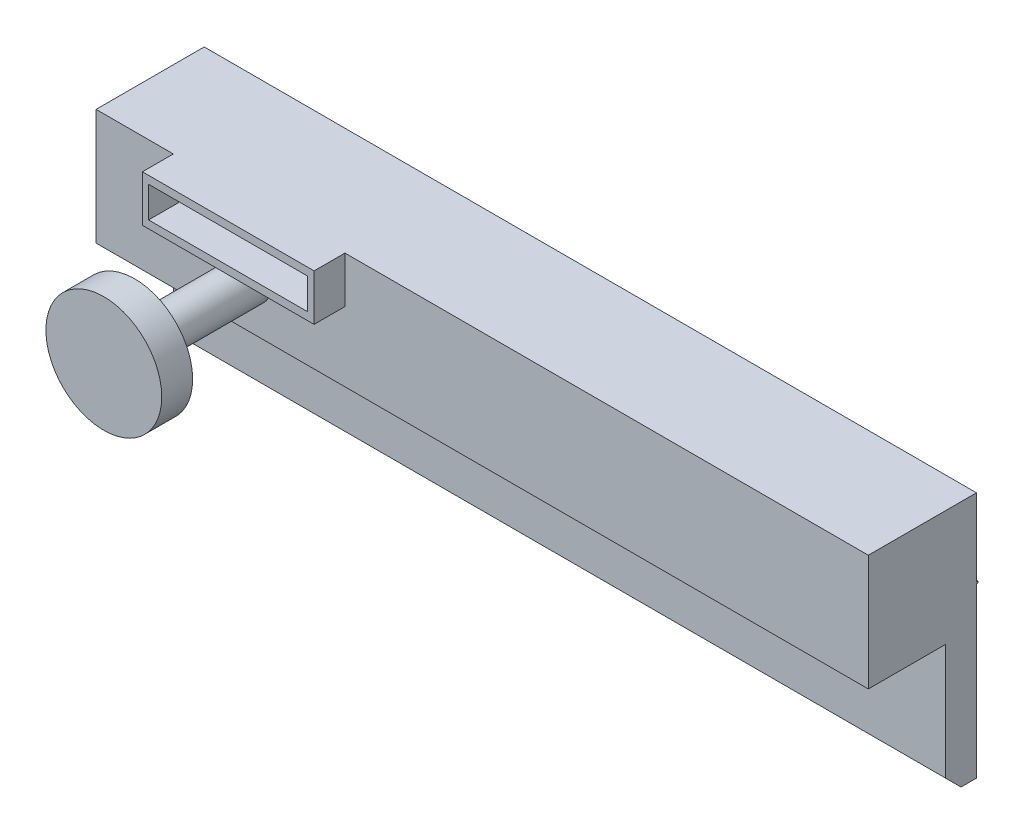
SolidWorks part; units mm, degrees
ref_plane "Front Plane" through (0, 0, 0) normal (0, 0, 1) x (1, 0, 0)
ref_plane "Top Plane" through (0, 0, 0) normal (0, 1, 0) x (1, 0, 0)
ref_plane "Right Plane" through (0, 0, 0) normal (1, 0, 0) x (0, 0, -1)
sketch "Sketch1" plane through (0, 0, 0) normal (0, 0, 1) x (1, 0, 0)
  line L1 (0, 0) -> (127, 0)
  line L2 (0, 0) -> (0, 40.64)
  line L3 (0, 40.64) -> (127, 40.64)
  line L4 (127, 0) -> (127, 40.64)
  dimension "D1" = 40.64
  dimension "D2" = 127
extrude "Boss-Extrude1" add sketch "Sketch1" along normal blind 5.08
chamfer "Chamfer3" distance 2.54 angle 45 1 edges at (63.5, 0, 5.08)
sketch "Sketch6" plane through (0, 0, 5.08) normal (0, 0, 1) x (1, 0, 0)
  line L0 (127, 2.54) -> (127, 40.64) construction
  line L1 (0, 40.64) -> (127, 40.64)
  line L2 (0, 40.64) -> (0, 21.59)
  line L3 (0, 21.59) -> (127, 21.59)
  line L4 (127, 40.64) -> (127, 21.59)
  dimension "D1" = 19.05
extrude "Boss-Extrude4" add sketch "Sketch6" along normal blind 12.7
sketch "Sketch14" plane through (0, 0, 17.78) normal (0, 0, 1) x (1, 0, 0)
  line L0 (0, 40.64) -> (0, 21.59) construction
  line L1 (0, 21.59) -> (127, 21.59) construction
  circle A0 centre (25.4, 29.21) radius 3.175
  dimension "D1" = 6.35
  dimension "D2" = 25.4
  dimension "D3" = 7.62
extrude "Boss-Extrude9" add sketch "Sketch14" along normal blind 19.05
sketch "Sketch15" plane through (0, 0, 36.83) normal (0, 0, 1) x (1, 0, 0)
  circle A0 centre (25.4, 29.21) radius 9.525
  dimension "D1" = 19.05
extrude "Boss-Extrude10" add sketch "Sketch15" along normal blind 5.08
sketch "Sketch16" plane through (0, 0, 17.78) normal (0, 0, 1) x (1, 0, 0)
  line L0 (127, 40.64) -> (0, 40.64) construction
  line L1 (12.7, 40.64) -> (40.9273, 40.64)
  line L2 (12.7, 40.64) -> (12.7, 33.02)
  line L3 (12.7, 33.02) -> (40.9273, 33.02)
  line L4 (40.9273, 40.64) -> (40.9273, 33.02)
  line L5 (0, 40.64) -> (0, 21.59) construction
  dimension "D1" = 7.62
  dimension "D2" = 0
  dimension "D3" = 12.7
extrude "Boss-Extrude11" add sketch "Sketch16" along normal blind 5.08
sketch "Sketch17" plane through (0, 0, 22.86) normal (0, 0, 1) x (1, 0, 0)
  line L0 (12.7, 33.02) -> (40.9273, 33.02) construction
  line L1 (13.716, 39.37) -> (39.8503, 39.37)
  line L2 (13.716, 39.37) -> (13.716, 34.29)
  line L3 (13.716, 34.29) -> (39.8503, 34.29)
  line L4 (39.8503, 39.37) -> (39.8503, 34.29)
  line L5 (0, 40.64) -> (0, 21.59) construction
  dimension "D1" = 5.08
  dimension "D2" = 26.1343
  dimension "D3" = 1.27
  dimension "D4" = 13.716
extrude "Cut-Extrude4" cut sketch "Sketch17" against normal blind 5.08
sketch "Sketch18" plane through (0, 0, 0) normal (0, 0, -1) x (-1, 0, 0)
  line L0 (-127, 0) -> (-127, 40.64) construction
  line L1 (-127, 27.94) -> (0, 27.94)
  line L2 (-127, 27.94) -> (-127, 27.686)
  line L3 (-127, 27.686) -> (0, 27.686)
  line L4 (0, 27.94) -> (0, 27.686)
  line L5 (0, 40.64) -> (0, 0) construction
  line L6 (-127, 40.64) -> (0, 40.64) construction
  dimension "D1" = 0.254
  dimension "D2" = 12.7
extrude "Boss-Extrude12" add sketch "Sketch18" along normal blind 0.254
